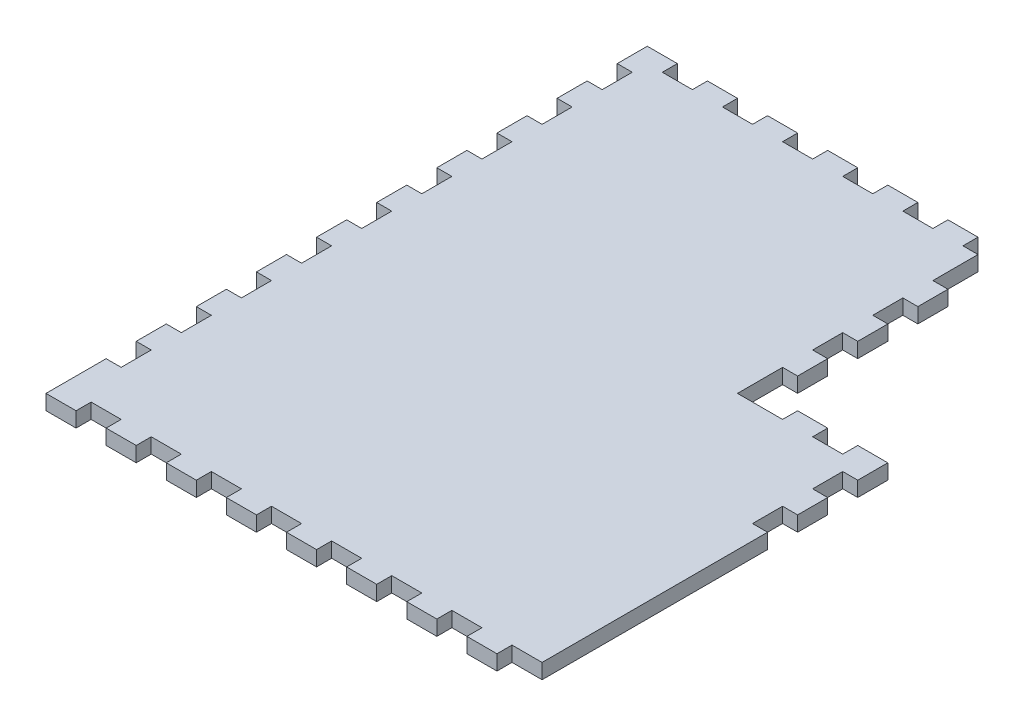
SolidWorks part; units mm, degrees
ref_plane "Front Plane" through (0, 0, 0) normal (0, 0, 1) x (1, 0, 0)
ref_plane "Top Plane" through (0, 0, 0) normal (0, 1, 0) x (1, 0, 0)
ref_plane "Right Plane" through (0, 0, 0) normal (1, 0, 0) x (0, 0, -1)
sketch "Sketch1" plane through (0, 0, 0) normal (0, 1, 0) x (1, 0, 0)
  line L1 (-101.6, 127) -> (101.6, 127)
  line L2 (-101.6, 127) -> (-101.6, -127)
  line L3 (-101.6, -127) -> (101.6, -127)
  line L4 (101.6, 127) -> (101.6, -127)
  line L5 (-101.6, 127) -> (101.6, -127) construction
  line L6 (-101.6, -127) -> (101.6, 127) construction
  point P0 (0, 0)
  dimension "D1" = 254
  dimension "D2" = 203.2
extrude "Boss-Extrude1" add sketch "Sketch1" along normal blind 6.35
sketch "Sketch2" plane through (0, 6.35, 0) normal (0, 1, 0) x (1, 0, 0)
  line L0 (101.6, 127) -> (-101.6, 127) construction
  line L1 (50.8, 127) -> (101.6, 127)
  line L2 (50.8, 127) -> (50.8, 25.4)
  line L3 (50.8, 25.4) -> (101.6, 25.4)
  line L4 (101.6, 127) -> (101.6, 25.4)
  line L5 (101.6, -127) -> (101.6, 127) construction
  dimension "D1" = 50.8
  dimension "D2" = 101.6
extrude "Cut-Extrude2" cut sketch "Sketch2" against normal through all
sketch "Sketch3" plane through (0, 6.35, 0) normal (0, 1, 0) x (1, 0, 0)
  line L1 (101.6, -127) -> (88.9, -127)
  line L2 (101.6, -127) -> (101.6, -120.65)
  line L3 (101.6, -120.65) -> (88.9, -120.65)
  line L4 (88.9, -127) -> (88.9, -120.65)
  dimension "D1" = 12.7
  dimension "D2" = 6.35
extrude "Cut-Extrude3" cut sketch "Sketch3" against normal through all
pattern_linear "LPattern1" count 8 spacing 25.4 along (-1, 0, 0) of "Cut-Extrude3"
sketch "Sketch4" plane through (0, 6.35, 0) normal (0, 1, 0) x (1, 0, 0)
  line L0 (-101.6, 127) -> (-101.6, -127) construction
  line L1 (-101.6, -101.6) -> (-95.25, -101.6)
  line L2 (-101.6, -101.6) -> (-101.6, -88.9)
  line L3 (-101.6, -88.9) -> (-95.25, -88.9)
  line L4 (-95.25, -101.6) -> (-95.25, -88.9)
  dimension "D1" = 6.35
  dimension "D2" = 12.7
  dimension "D3" = 25.4
extrude "Cut-Extrude4" cut sketch "Sketch4" against normal through all
pattern_linear "LPattern2" count 9 spacing 25.4 along (0, 0, -1) of "Cut-Extrude4"
sketch "Sketch5" plane through (0, 6.35, 0) normal (0, 1, 0) x (1, 0, 0)
  line L1 (50.8, 127) -> (38.1, 127)
  line L2 (50.8, 127) -> (50.8, 120.65)
  line L3 (50.8, 120.65) -> (38.1, 120.65)
  line L4 (38.1, 127) -> (38.1, 120.65)
  dimension "D1" = 6.35
  dimension "D2" = 12.7
extrude "Cut-Extrude5" cut sketch "Sketch5" against normal through all
pattern_linear "LPattern3" count 6 spacing 25.4 along (-1, 0, 0) of "Cut-Extrude5"
sketch "Sketch7" plane through (0, 6.35, 0) normal (0, 1, 0) x (1, 0, 0)
  line L0 (101.6, -120.65) -> (101.6, 25.4) construction
  line L1 (101.6, 12.7) -> (95.25, 12.7)
  line L2 (101.6, 12.7) -> (101.6, 0)
  line L3 (101.6, 0) -> (95.25, 0)
  line L4 (95.25, 12.7) -> (95.25, 0)
  dimension "D1" = 6.35
  dimension "D2" = 12.7
  dimension "D3" = 12.7
extrude "Cut-Extrude8" cut sketch "Sketch7" against normal through all
pattern_linear "LPattern5" count 2 spacing 25.4 along (0, 0, 1) of "Cut-Extrude8"
sketch "Sketch8" plane through (0, 6.35, 0) normal (0, 1, 0) x (1, 0, 0)
  line L0 (50.8, 25.4) -> (101.6, 25.4) construction
  line L1 (88.9, 25.4) -> (76.2, 25.4)
  line L2 (88.9, 25.4) -> (88.9, 19.05)
  line L3 (88.9, 19.05) -> (76.2, 19.05)
  line L4 (76.2, 25.4) -> (76.2, 19.05)
  dimension "D1" = 6.35
  dimension "D2" = 12.7
  dimension "D3" = 12.7
extrude "Cut-Extrude9" cut sketch "Sketch8" against normal through all
pattern_linear "LPattern6" count 2 spacing 25.4 along (-1, 0, 0) of "Cut-Extrude9"
sketch "Sketch9" plane through (0, 6.35, 0) normal (0, 1, 0) x (1, 0, 0)
  line L1 (50.8, 120.65) -> (44.45, 120.65)
  line L2 (50.8, 120.65) -> (50.8, 101.6)
  line L3 (50.8, 101.6) -> (44.45, 101.6)
  line L4 (44.45, 120.65) -> (44.45, 101.6)
  dimension "D1" = 6.35
  dimension "D2" = 19.05
extrude "Cut-Extrude10" cut sketch "Sketch9" against normal through all
sketch "Sketch10" plane through (0, 6.35, 0) normal (0, 1, 0) x (1, 0, 0)
  line L0 (50.8, 101.6) -> (50.8, 19.05) construction
  line L1 (50.8, 88.9) -> (44.45, 88.9)
  line L2 (50.8, 88.9) -> (50.8, 76.2)
  line L3 (50.8, 76.2) -> (44.45, 76.2)
  line L4 (44.45, 88.9) -> (44.45, 76.2)
  dimension "D1" = 6.35
  dimension "D2" = 12.7
  dimension "D3" = 12.7
extrude "Cut-Extrude11" cut sketch "Sketch10" against normal through all
pattern_linear "LPattern7" count 3 spacing 25.4 along (0, 0, 1) of "Cut-Extrude11"
sketch "Sketch11" plane through (0, 6.35, 0) normal (0, 1, 0) x (1, 0, 0)
  line L1 (50.8, 25.4) -> (44.45, 25.4)
  line L2 (50.8, 25.4) -> (50.8, 19.05)
  line L3 (50.8, 19.05) -> (44.45, 19.05)
  line L4 (44.45, 25.4) -> (44.45, 19.05)
  dimension "D1" = 6.35
  dimension "D2" = 6.35
extrude "Cut-Extrude12" cut sketch "Sketch11" against normal through all
